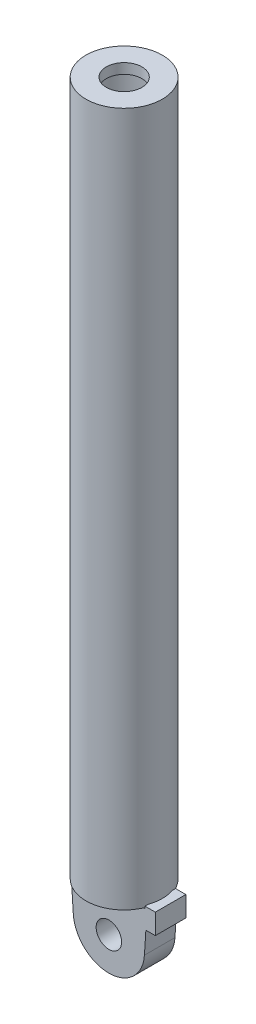
SolidWorks part; units mm, degrees
material "Plain Carbon Steel"
ref_plane "Front Plane" through (0, 0, 0) normal (0, 0, 1) x (1, 0, 0)
ref_plane "Top Plane" through (0, 0, 0) normal (0, 1, 0) x (1, 0, 0)
ref_plane "Right Plane" through (0, 0, 0) normal (1, 0, 0) x (0, 0, -1)
sketch "Sketch1" plane through (0, 0, 0) normal (0, 0, 1) x (1, 0, 0)
  line L0 (37.5, 40) -> (37.5, 722) construction
  line L1 (37.6286, 42) -> (35.5, 42)
  line L2 (37.6286, 42) -> (45.6286, 42)
  line L3 (45.6286, 42) -> (45.6286, 22)
  line L4 (45.6286, 22) -> (36.3425, 22)
  line L5 (37.5, 40) -> (-37.5, 40) construction
  line L6 (37.5, 722) -> (-37.5, 722) construction
  line L7 (-37.5, 40) -> (-37.5, 722) construction
  line L8 (37.5, 40) -> (34.9279, 0) construction
  line L9 (-37.5, 40) -> (-34.9279, 0)
  line L10 (0, 40) -> (0, -105.1053) construction
  line L11 (34.9279, 0) -> (-34.9279, 0) construction
  line L12 (0, 722) -> (0, 40) construction
  line L13 (37.5, 172) -> (-37.5, 172) construction
  line L14 (36.3425, 22) -> (34.9279, 0)
  line L15 (-37.5, 40) -> (35.5, 40)
  line L16 (45.6286, 32) -> (39.38, 32) construction
  line L17 (35.5, 42) -> (35.5, 40)
  arc A0 (-34.9279, 0) -> (34.9279, 0) centre (0, 2.246) ccw
  circle A1 centre (0, 0) radius 12.5
  dimension "D2" = 35
  dimension "D3" = 25
  dimension "D1" = 75
  dimension "D4" = 40
  dimension "D5" = 722
  dimension "D6" = 550
  dimension "D7" = 20
  dimension "D8" = 32
  dimension "D9" = 2
  dimension "D11" = 8
extrude "Boss-Extrude1" add sketch "Sketch1" along normal mid plane 30
sketch "Sketch2" plane through (0, 0, 0) normal (0, 0, 1) x (1, 0, 0)
  line L0 (37.5, 40) -> (37.5, 722) construction
  line L1 (37.5, 40) -> (-37.5, 40) construction
  line L2 (37.5, 722) -> (-37.5, 722) construction
  line L3 (-37.5, 40) -> (-37.5, 722) construction
  line L4 (37.5, 40) -> (34.9279, 0) construction
  line L5 (-37.5, 40) -> (-34.9279, 0) construction
  line L6 (0, 40) -> (0, -109.9514) construction
  line L7 (34.9279, 0) -> (-34.9279, 0) construction
  line L8 (0, 722) -> (0, 40) construction
  line L9 (37.5, 172) -> (-37.5, 172) construction
  line L10 (-37.5, 722) -> (-17.5, 722)
  line L11 (-17.5, 722) -> (-17.5, 712)
  line L12 (-17.5, 712) -> (-32.5, 712)
  line L13 (-32.5, 712) -> (-32.5, 172)
  line L14 (-32.5, 172) -> (0, 172)
  line L15 (0, 172) -> (0, 40)
  line L16 (0, 40) -> (-37.5, 40)
  line L17 (-37.5, 40) -> (-37.5, 722)
  arc A0 (-34.9279, 0) -> (34.9279, 0) centre (0, 2.246) ccw construction
  circle A1 centre (0, 0) radius 12.5 construction
  dimension "D2" = 35
  dimension "D3" = 25
  dimension "D1" = 75
  dimension "D4" = 40
  dimension "D5" = 722
  dimension "D6" = 550
  dimension "D7" = 5
  dimension "D8" = 17.5
  dimension "D10" = 10
revolve "Revolve1" add sketch "Sketch2" angle 360 about L8
ref_point "Point1"
